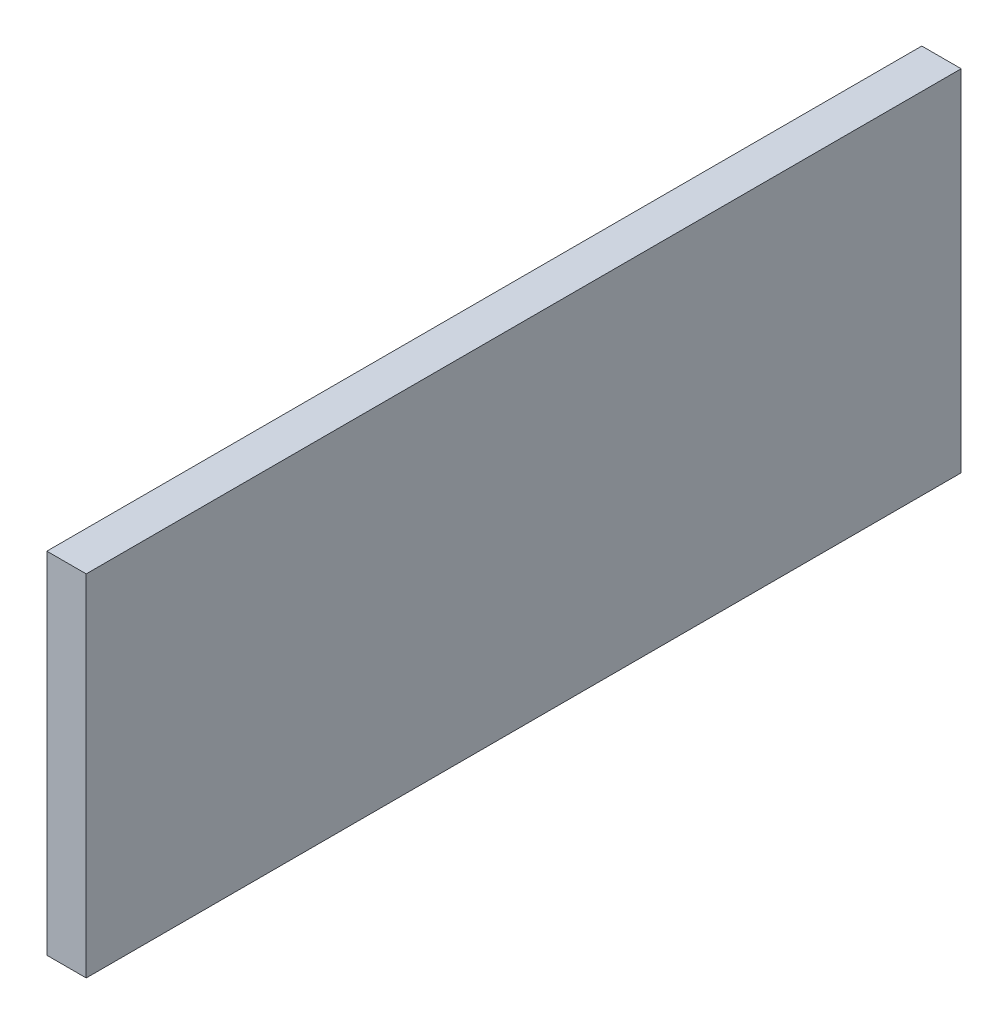
SolidWorks part; units mm, degrees
ref_plane "Front Plane" through (0, 0, 0) normal (0, 0, 1) x (1, 0, 0)
ref_plane "Top Plane" through (0, 0, 0) normal (0, 1, 0) x (1, 0, 0)
ref_plane "Right Plane" through (0, 0, 0) normal (1, 0, 0) x (0, 0, -1)
sketch "Sketch1" plane through (0, 0, 0) normal (1, 0, 0) x (0, 0, -1)
  line L1 (-29.0143, 7.2536) -> (370.9857, 7.2536)
  line L2 (-29.0143, 7.2536) -> (-29.0143, -152.7464)
  line L3 (-29.0143, -152.7464) -> (370.9857, -152.7464)
  line L4 (370.9857, 7.2536) -> (370.9857, -152.7464)
  dimension "D1" = 400
  dimension "D2" = 160
extrude "Boss-Extrude1" add sketch "Sketch1" along normal blind 18
